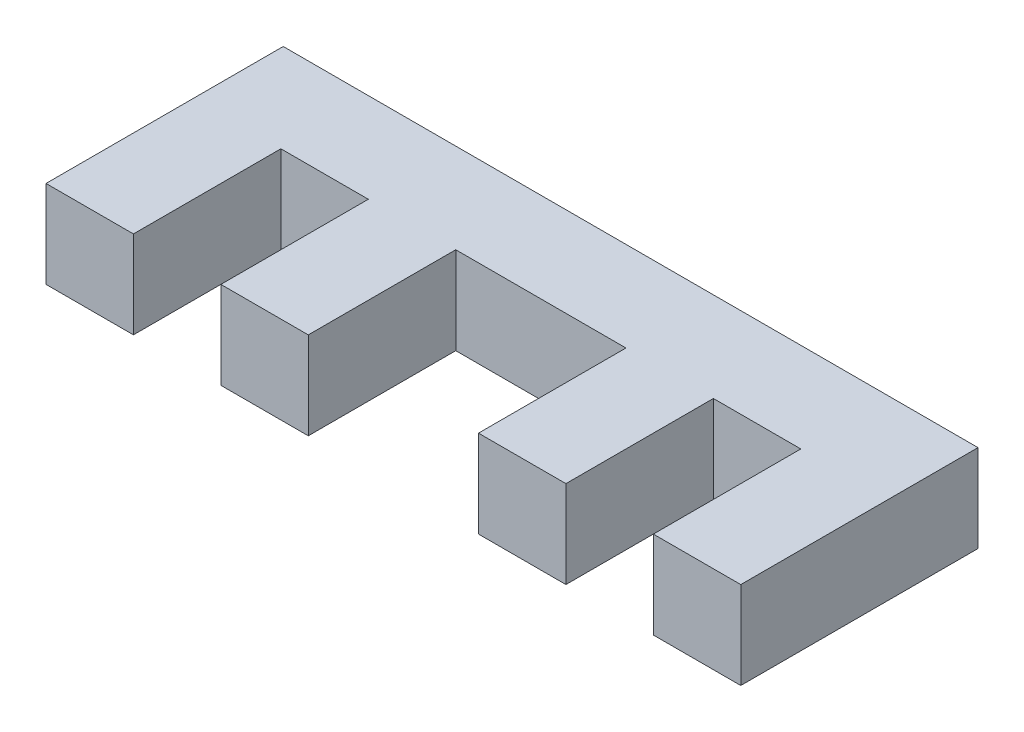
SolidWorks part; units mm, degrees
ref_plane "Front Plane" through (0, 0, 0) normal (0, 0, 1) x (1, 0, 0)
ref_plane "Top Plane" through (0, 0, 0) normal (0, 1, 0) x (1, 0, 0)
ref_plane "Right Plane" through (0, 0, 0) normal (1, 0, 0) x (0, 0, -1)
sketch "Sketch1" plane through (0, 0, 0) normal (0, 1, 0) x (1, 0, 0)
  line L0 (0, 0) -> (3.175, 0)
  line L1 (3.175, 0) -> (3.175, 5.3552)
  line L2 (3.175, 5.3552) -> (6.35, 5.3552)
  line L3 (15.7057, 5.3552) -> (15.7057, 0)
  line L4 (15.7057, 0) -> (18.8807, 0)
  line L5 (18.8807, 0) -> (18.8807, 5.3552)
  line L6 (18.8807, 5.3552) -> (22.0557, 5.3552)
  line L7 (22.0557, 5.3552) -> (22.0557, 0)
  line L8 (22.0557, 0) -> (25.2307, 0)
  line L9 (25.2307, 0) -> (25.2307, 8.6148)
  line L10 (25.2307, 8.6148) -> (0, 8.6148)
  line L11 (0, 8.6148) -> (0, 0)
  line L12 (6.35, 5.3552) -> (6.35, 0)
  line L13 (6.35, 0) -> (9.525, 0)
  line L14 (9.525, 0) -> (9.525, 5.3552)
  line L15 (9.525, 5.3552) -> (15.7057, 5.3552)
  dimension "D1" = 3.175
  dimension "D2" = 3.175
extrude "Boss-Extrude1" add sketch "Sketch1" along normal blind 3.175
